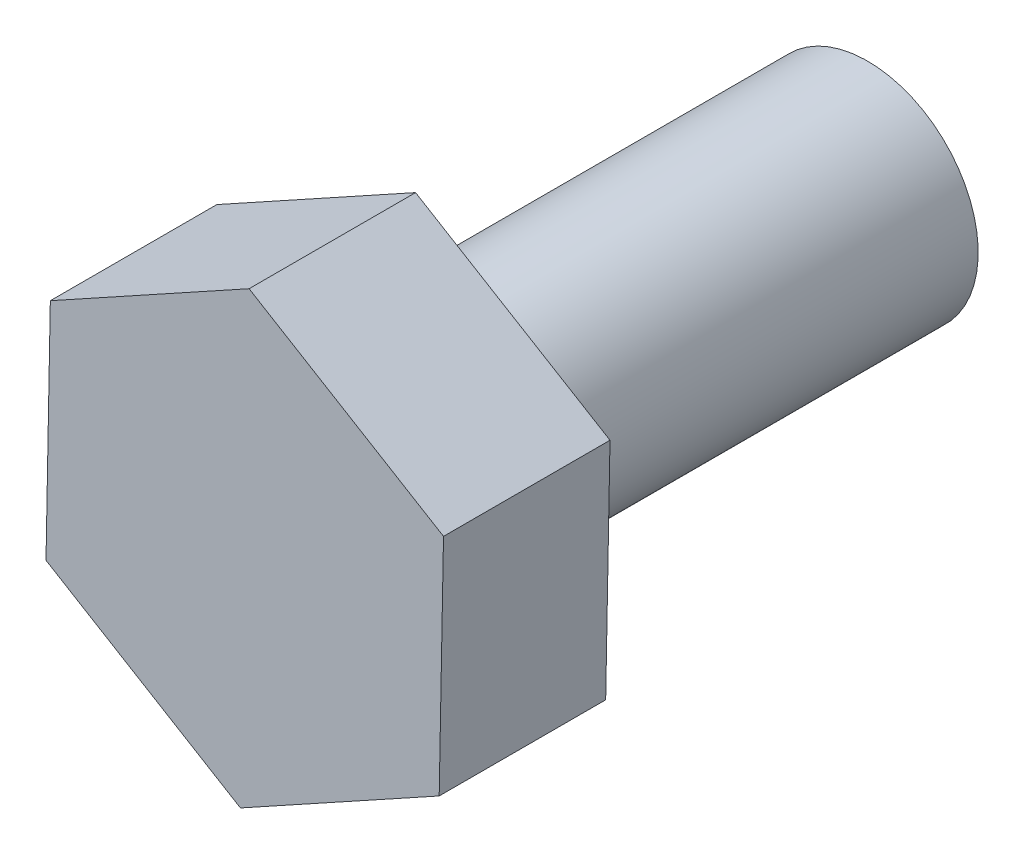
SolidWorks part; units mm, degrees
ref_plane "Спереди" through (0, 0, 0) normal (0, 0, 1) x (1, 0, 0)
ref_plane "Сверху" through (0, 0, 0) normal (0, 1, 0) x (1, 0, 0)
ref_plane "Справа" through (0, 0, 0) normal (1, 0, 0) x (0, 0, -1)
sketch "Эскиз1" plane through (0, 0, 0) normal (0, 0, 1) x (1, 0, 0)
  line L1 (3.3809, -1.9624) -> (3.4563, 1.9918)
  line L2 (3.4563, 1.9918) -> (0.0696, 4.0341)
  line L3 (0.0696, 4.0341) -> (-3.3924, 2.1223)
  line L4 (-3.3924, 2.1223) -> (-3.4678, -1.8318)
  line L5 (-3.4678, -1.8318) -> (-0.0811, -3.8741)
  line L6 (-0.0811, -3.8741) -> (3.3809, -1.9624)
  circle A0 centre (-0.0057, 0.08) radius 3.425 construction
  dimension "D1" = 6.85
extrude "Бобышка-Вытянуть1" add sketch "Эскиз1" against normal blind 2.9
sketch "Эскиз4" plane through (0, 0, -2.9) normal (0, 0, -1) x (-1, 0, 0)
  line L0 (-0.0696, 4.0341) -> (3.3924, 2.1223) construction
  line L1 (3.4678, -1.8318) -> (0.0811, -3.8741) construction
  circle A0 centre (0.0057, 0.08) radius 1.925
  point P6 (0.2221, 2.3165)
  point P7 (0.2221, 2.3165)
  dimension "D1" = 3.425
  dimension "D2" = 3.425
extrude "Бобышка-Вытянуть2" add sketch "Эскиз4" along normal blind 7.95
